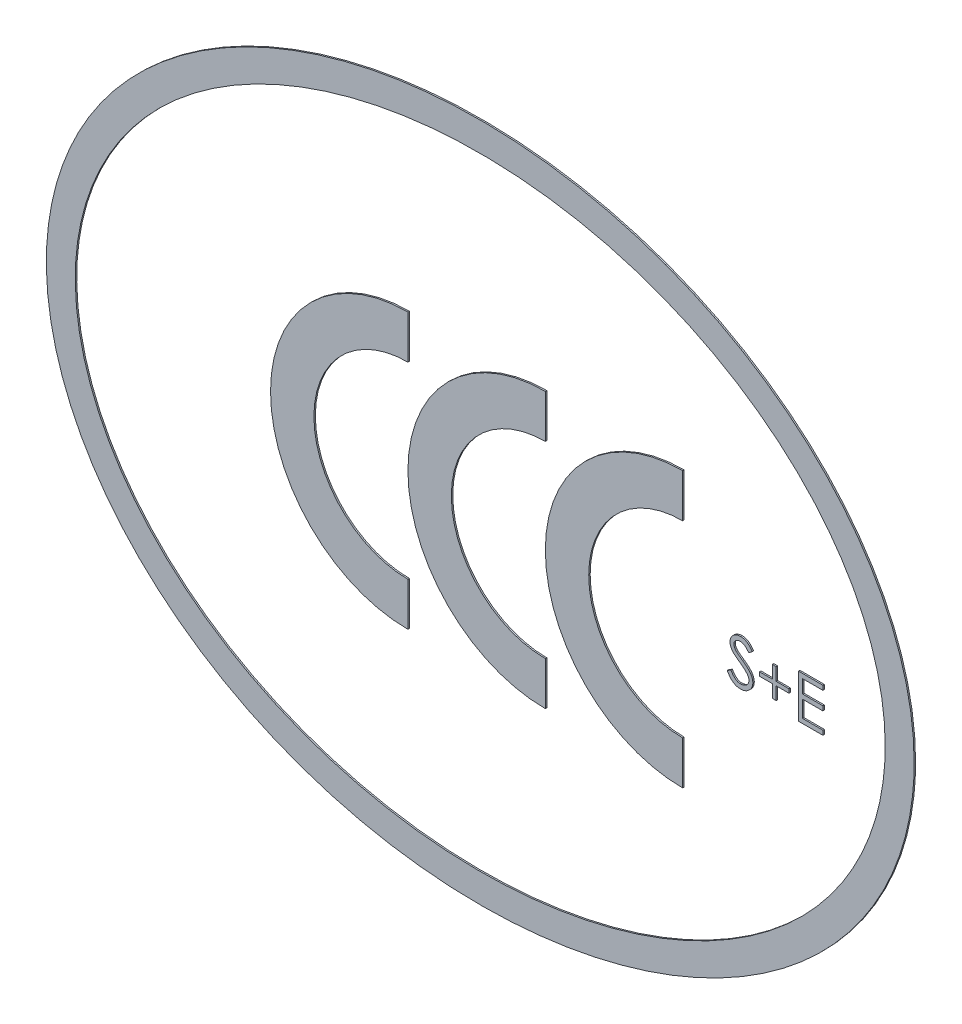
SolidWorks part; units mm, degrees
ref_plane "Vorne" through (0, 0, 0) normal (0, 0, 1) x (1, 0, 0)
ref_plane "Oben" through (0, 0, 0) normal (0, 1, 0) x (1, 0, 0)
ref_plane "Rechts" through (0, 0, 0) normal (1, 0, 0) x (0, 0, -1)
sketch "Skizze1" plane through (0, 0, 0) normal (0, 0, 1) x (1, 0, 0)
  line L0 (-30, 0) -> (30, 0) construction
  line L1 (0, 23.5) -> (0, -23.5) construction
  line L2 (14, -9.5) -> (14, -6.5)
  line L3 (14, 6.5) -> (14, 9.5)
  line L4 (4.5, -9.5) -> (4.5, -6.5)
  line L5 (-5, -9.5) -> (-5, -6.5)
  line L6 (-5, 6.5) -> (-5, 9.5)
  line L7 (4.5, 6.5) -> (4.5, 9.5)
  arc A0 (14, 9.5) -> (14, -9.5) centre (14, 0) ccw
  arc A1 (14, 6.5) -> (14, -6.5) centre (14, 0) ccw
  arc A2 (-5, 9.5) -> (-5, -9.5) centre (-5, 0) ccw
  arc A3 (-5, 6.5) -> (-5, -6.5) centre (-5, 0) ccw
  arc A4 (4.5, 9.5) -> (4.5, -9.5) centre (4.5, 0) ccw
  arc A6 (4.5, 6.5) -> (4.5, -6.5) centre (4.5, 0) ccw
  ellipse E0 centre (0, 0) end of major axis (30, 0) minor radius 23.5
  ellipse E1 centre (0, 0) end of major axis (28, 0) minor radius 21.5
  dimension "D5" = 3
  dimension "D6" = 19
  dimension "D1" = 47
  dimension "D2" = 60
  dimension "D3" = 2
  dimension "D4" = 2
  dimension "D7" = 14
  dimension "D8" = 9.5
  dimension "D9" = 9.5
extrude "Aufsatz-Linear austragen1" add sketch "Skizze1" along normal blind 0.1 contours E0 E1 | A3 L6 A2 L5 | A6 L7 A4 L4 | A1 L3 A0 L2
sketch "Skizze4" plane through (0, 0, 0) normal (0, 0, 1) x (1, 0, 0)
  line L0 (-30, 0) -> (30, 0) construction
  line L1 (0, 23.5) -> (0, -23.5) construction
  text T0 "S+E" font "Century Gothic" height 3
  dimension "D1" = 1.5
  dimension "D2" = 17
extrude "Aufsatz-Linear austragen2" add sketch "Skizze4" along normal blind 0.1 separate body
